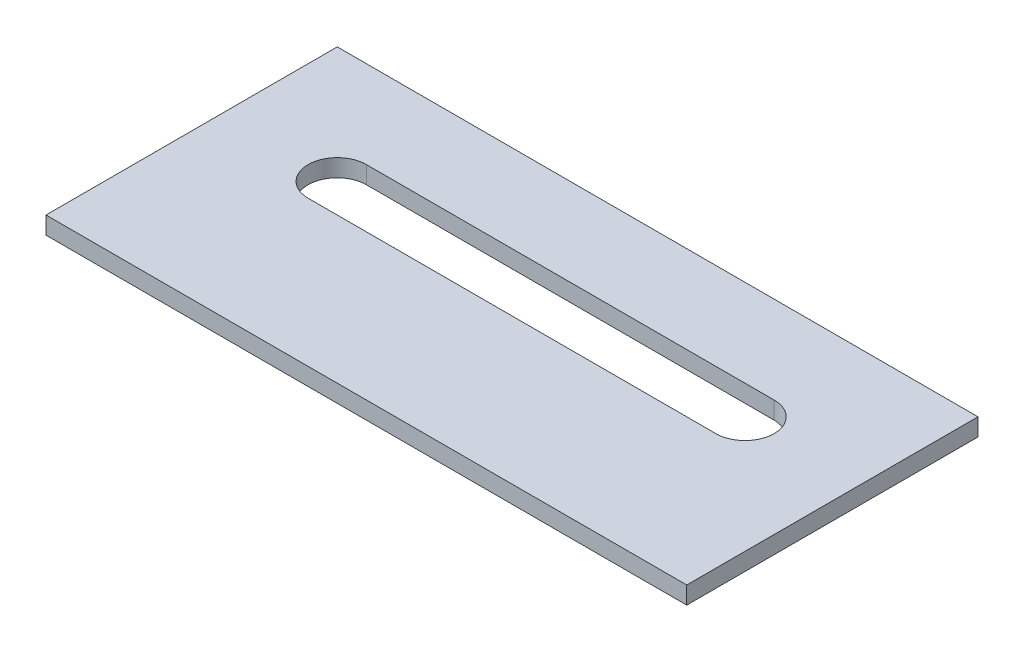
SolidWorks part; units mm, degrees
ref_plane "Ön Düzlem" through (0, 0, 0) normal (0, 0, 1) x (1, 0, 0)
ref_plane "Üst Düzlem" through (0, 0, 0) normal (0, 1, 0) x (1, 0, 0)
ref_plane "Sağ Düzlem" through (0, 0, 0) normal (1, 0, 0) x (0, 0, -1)
sketch "Çizim1" plane through (0, 0, 0) normal (0, 1, 0) x (1, 0, 0)
  line L0 (20, -20) -> (90, -20) construction
  line L1 (0, 0) -> (110, 0)
  line L2 (0, 0) -> (0, -50)
  line L3 (0, -50) -> (110, -50)
  line L4 (110, 0) -> (110, -50)
  line L5 (20, -15) -> (90, -15)
  line L6 (20, -25) -> (90, -25)
  arc A0 (20, -15) -> (20, -25) centre (20, -20) ccw
  arc A1 (90, -25) -> (90, -15) centre (90, -20) ccw
  point P7 (55, -20)
  dimension "D5" = 20
  dimension "D6" = 20
  dimension "D1" = 110
  dimension "D2" = 50
  dimension "D3" = 10
  dimension "D4" = 25
extrude "Yükseklik-Ekstrüzyon1" add sketch "Çizim1" along normal blind 3
